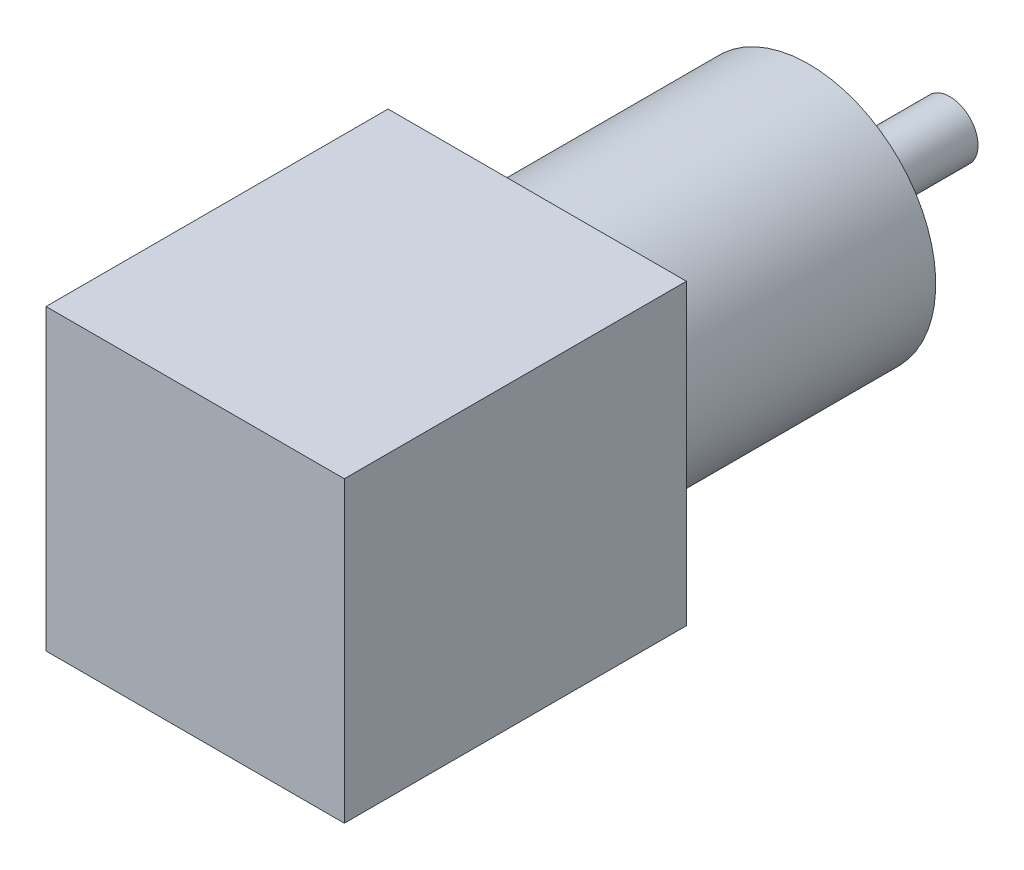
SolidWorks part; units mm, degrees
ref_plane "Front Plane" through (0, 0, 0) normal (0, 0, 1) x (1, 0, 0)
ref_plane "Top Plane" through (0, 0, 0) normal (0, 1, 0) x (1, 0, 0)
ref_plane "Right Plane" through (0, 0, 0) normal (1, 0, 0) x (0, 0, -1)
sketch "Sketch1" plane through (0, 0, 0) normal (0, 0, 1) x (1, 0, 0)
  line L1 (-21.15, 21.15) -> (21.15, 21.15)
  line L2 (-21.15, 21.15) -> (-21.15, -21.15)
  line L3 (-21.15, -21.15) -> (21.15, -21.15)
  line L4 (21.15, 21.15) -> (21.15, -21.15)
  line L5 (-21.15, 21.15) -> (21.15, -21.15) construction
  line L6 (-21.15, -21.15) -> (21.15, 21.15) construction
  point P0 (0, 0)
  dimension "D1" = 42.3
  dimension "D2" = 42.3
extrude "Boss-Extrude1" add sketch "Sketch1" along normal blind 48.5
sketch "Sketch3" plane through (0, 0, 0) normal (0, 0, -1) x (-1, 0, 0)
  circle A0 centre (0, 0) radius 18
  dimension "D1" = 36
extrude "Boss-Extrude2" add sketch "Sketch3" along normal blind 38.5
sketch "Sketch5" plane through (0, 0, -38.5) normal (0, 0, -1) x (-1, 0, 0)
  circle A0 centre (0, 0) radius 4
  dimension "D1" = 8
extrude "Boss-Extrude3" add sketch "Sketch5" along normal blind 20
sketch "Sketch6" plane through (0, 0, -38.5) normal (0, 0, -1) x (-1, 0, 0)
  line L0 (0, 18.8487) -> (0, -15.8106) construction
  line L1 (-14.9567, 0) -> (15.3246, 0) construction
  line L2 (0, 0) -> (-17.5725, 17.5725) construction
  circle A0 centre (-10.6066, 10.6066) radius 1.5
  circle A1 centre (10.6066, 10.6066) radius 1.5
  circle A2 centre (10.6066, -10.6066) radius 1.5
  circle A3 centre (-10.6066, -10.6066) radius 1.5
  dimension "D1" = 3
  dimension "D2" = 15
  dimension "D3" = 45
extrude "Cut-Extrude1" cut sketch "Sketch6" against normal blind 10
